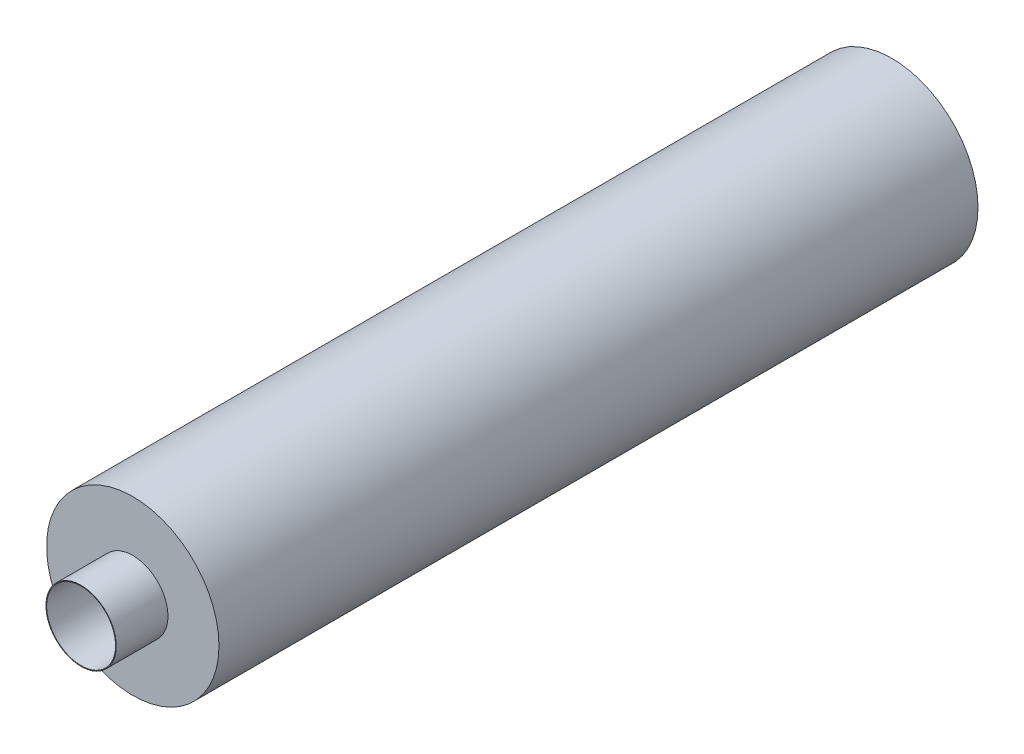
SolidWorks part; units mm, degrees
ref_plane "Front Plane" through (0, 0, 0) normal (0, 0, 1) x (1, 0, 0)
ref_plane "Top Plane" through (0, 0, 0) normal (0, 1, 0) x (1, 0, 0)
ref_plane "Right Plane" through (0, 0, 0) normal (1, 0, 0) x (0, 0, -1)
sketch "Sketch1" plane through (0, 0, 0) normal (0, 0, 1) x (1, 0, 0)
  circle A0 centre (0, 0) radius 250
  dimension "D1" = 500
extrude "Boss-Extrude1" add sketch "Sketch1" along normal blind 2200
shell "Shell1" thickness 2
sketch "Sketch10" plane through (0, 0, 2200) normal (0, 0, 1) x (1, 0, 0)
  circle A0 centre (0, 0) radius 100
  circle A1 centre (0, 0) radius 250
  circle A2 centre (0, 0) radius 250
  dimension "D2" = 200
  dimension "D1" = 0
extrude "Boss-Extrude4" add sketch "Sketch10" along normal blind 2
sketch "Sketch11" plane through (0, 0, 2202) normal (0, 0, 1) x (1, 0, 0)
  circle A0 centre (0, 0) radius 100 construction
  circle A3 centre (0, 0) radius 100
extrude "Extrude-Thin2" add sketch "Sketch11" along normal blind 150 thin
